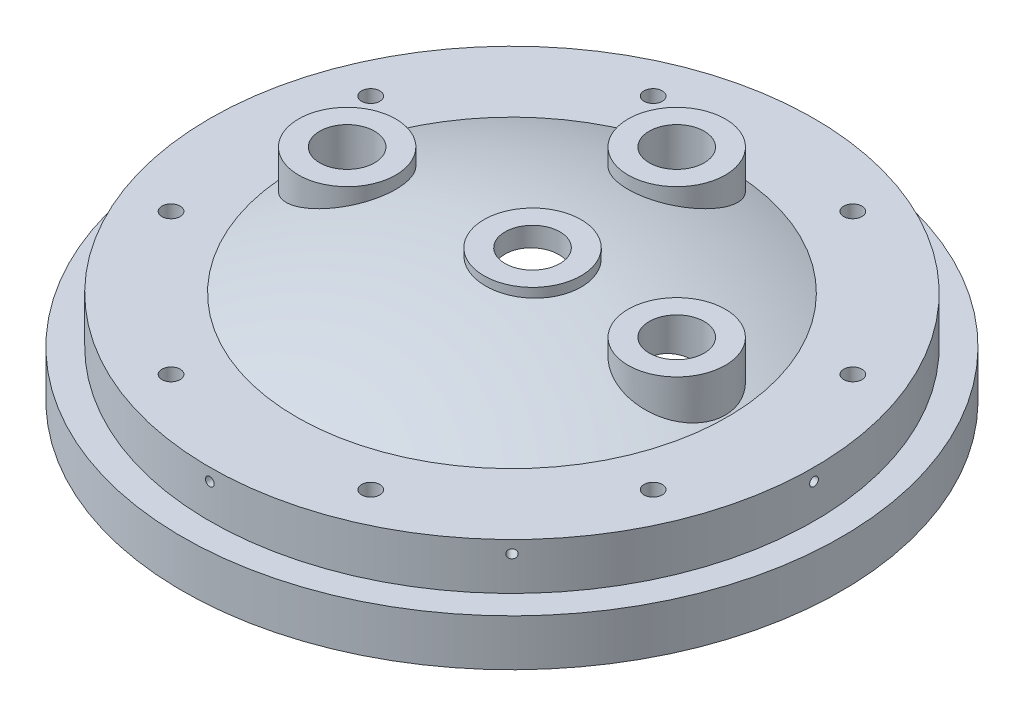
SolidWorks part; units mm, degrees
material "6061-T6 (SS)"
ref_plane "Front Plane" through (0, 0, 0) normal (0, 0, 1) x (1, 0, 0)
ref_plane "Top Plane" through (0, 0, 0) normal (0, 1, 0) x (1, 0, 0)
ref_plane "Right Plane" through (0, 0, 0) normal (1, 0, 0) x (0, 0, -1)
sketch "Sketch1" plane through (0, 0, 0) normal (0, 0, 1) x (1, 0, 0)
  line L0 (146.05, 0) -> (152.4, 0)
  line L1 (152.4, 0) -> (152.4, 21.59)
  line L2 (152.4, 21.59) -> (139.7, 21.59)
  line L3 (139.7, 21.59) -> (139.7, 43.18)
  line L4 (0, 63.5) -> (0, 57.15)
  line L5 (146.05, 0) -> (146.05, 9.4998)
  line L6 (139.7, 43.18) -> (99.5473, 43.18)
  arc A0 (0, 63.5) -> (99.5473, 43.18) centre (0, -190.5) cw
  arc A1 (0, 57.15) -> (146.05, 9.4998) centre (0, -190.5) cw
  point P2 (0, 0)
  point P9 (0, 0)
  point P12 (146.05, 3.8905)
  point P14 (0, 0)
  dimension "D1" = 152.4
  dimension "D2" = 6.35
  dimension "D7" = 247.65
  dimension "D3" = 12.7
  dimension "D4" = 21.59
  dimension "D5" = 43.18
  dimension "D6" = 6.35
  dimension "D8" = 63.5
revolve "Revolve1" add sketch "Sketch1" angle 360 about L4
ref_plane "Plane1" through (139.7, 0, 0) normal (1, 0, 0) x (0, 0, -1)
hole_wizard "Tap Drill for #10-32 Tap1" positions "Sketch4" profile "Sketch5" hole size "#10-32" standard "ANSI Inch"
sketch "Sketch4" plane through (139.7, 0, 0) normal (1, 0, 0) x (0, 0, -1)
  line L0 (152.4, 21.59) -> (-152.4, 21.59) construction
  point P0 (0, 37.465)
  dimension "D1" = 15.875
sketch "Sketch5" plane through (139.7, 37.465, 0) normal (0, 1, 0) x (0, 0, -1)
  line L0 (0, 0) -> (0, 11.3733)
  line L1 (0, 11.3733) -> (2.0193, 10.16)
  line L2 (2.0193, 10.16) -> (2.0193, 0)
  line L5 (2.0193, 0) -> (0, 0)
  line L10 (0, 11.3733) -> (-2.0193, 10.16) construction
  line L11 (0, -6.35) -> (0, 107.95) construction
  dimension "Hole Dia." = 4.0386
  dimension "Hole Depth" = 10.16
  dimension "Drill Angle" = 118
pattern_circular "CirPattern1" count 8 over 360 about axis through (0, 21.59, 0) along (0, 1, 0) of "Tap Drill for #10-32 Tap1"
ref_plane "Plane2" through (0, 63.5, 0) normal (0, 1, 0) x (1, 0, 0)
sketch "Sketch8" plane through (0, 63.5, 0) normal (0, 1, 0) x (1, 0, 0)
  line L0 (9.525, 0) -> (0, 0) construction
  circle A0 centre (9.525, 0) radius 22.479
  dimension "D1" = 44.958
  dimension "D2" = 9.525
extrude "Boss-Extrude1" add sketch "Sketch8" along normal blind 2.54 and the other way up to next
sketch "Sketch9" plane through (0, 63.5, 0) normal (0, 1, 0) x (1, 0, 0)
  line L0 (76.2, 0) -> (9.525, 0) construction
  circle A0 centre (76.2, 0) radius 22.479
  dimension "D1" = 76.2
  dimension "D2" = 44.958
extrude "Boss-Extrude2" add sketch "Sketch9" against normal up to next
hole_wizard "Hole1" positions "Sketch10" profile "Sketch12" legacy
sketch "Sketch10" plane through (0, 66.04, 0) normal (0, 1, 0) x (1, 0, 0)
  point P6 (9.525, 0)
sketch "Sketch12" plane through (9.525, 66.04, 0) normal (1, 0, 0) x (0, 0, 1)
  line L0 (0, 0) -> (0, 25.4)
  line L1 (0, 25.4) -> (12.7, 25.4)
  line L2 (12.7, 25.4) -> (12.7, 0)
  line L3 (12.7, 0) -> (0, 0)
  line L4 (0, 110) -> (0, -10) construction
  dimension "Diameter" = 25.4
  dimension "Depth" = 25.4
hole_wizard "Hole2" positions "Sketch14" profile "Sketch15" legacy
sketch "Sketch14" plane through (0, 63.5, 0) normal (0, 1, 0) x (1, 0, 0)
  point P0 (76.2, 0)
sketch "Sketch15" plane through (76.2, 63.5, 0) normal (1, 0, 0) x (0, 0, 1)
  line L0 (0, 0) -> (0, 25.4)
  line L1 (0, 25.4) -> (12.7, 25.4)
  line L2 (12.7, 25.4) -> (12.7, 0)
  line L3 (12.7, 0) -> (0, 0)
  line L4 (0, 110) -> (0, -10) construction
  dimension "Diameter" = 25.4
  dimension "Depth" = 25.4
pattern_circular "CirPattern2" count 3 every 90 about axis through (0, 0, 0) along (0, 1, 0) of "Hole2", "Boss-Extrude2"
hole_wizard "3/8-24 Tapped Hole1" positions "Sketch17" profile "Sketch19" tap size "3/8-24" standard "ANSI Inch"
sketch "Sketch17" plane through (0, 43.18, 0) normal (0, 1, 0) x (1, 0, 0)
  line L0 (111.4661, 46.1708) -> (0, 0)
  line L2 (0, 0) -> (139.7, 0)
  circle A0 centre (0, 0) radius 139.7 construction
  point P0 (111.4661, 46.1708)
  dimension "D1" = 22.5
  dimension "D2" = 120.65
sketch "Sketch19" plane through (111.4661, 43.18, -46.1708) normal (1, 0, 0) x (0, 0, 1)
  line L0 (0, 0) -> (0, 11.4235)
  line L1 (0, 11.4235) -> (4.2164, 8.89)
  line L2 (4.2164, 8.89) -> (4.2164, 0)
  line L5 (4.2164, 0) -> (0, 0)
  line L10 (0, 11.4235) -> (-4.2164, 8.89) construction
  line L11 (0, -6.35) -> (0, 107.95) construction
  dimension "Tap Drill Dia." = 8.4328
  dimension "Tap Drill Depth" = 8.89
  dimension "Drill Angle" = 118
cosmetic thread "Hole Thread1" parameters "D1"=8.89, "D2"=9.525
pattern_circular "CirPattern3" count 8 over 360 about axis through (0, 0, 0) along (0, 1, 0) of "3/8-24 Tapped Hole1"
